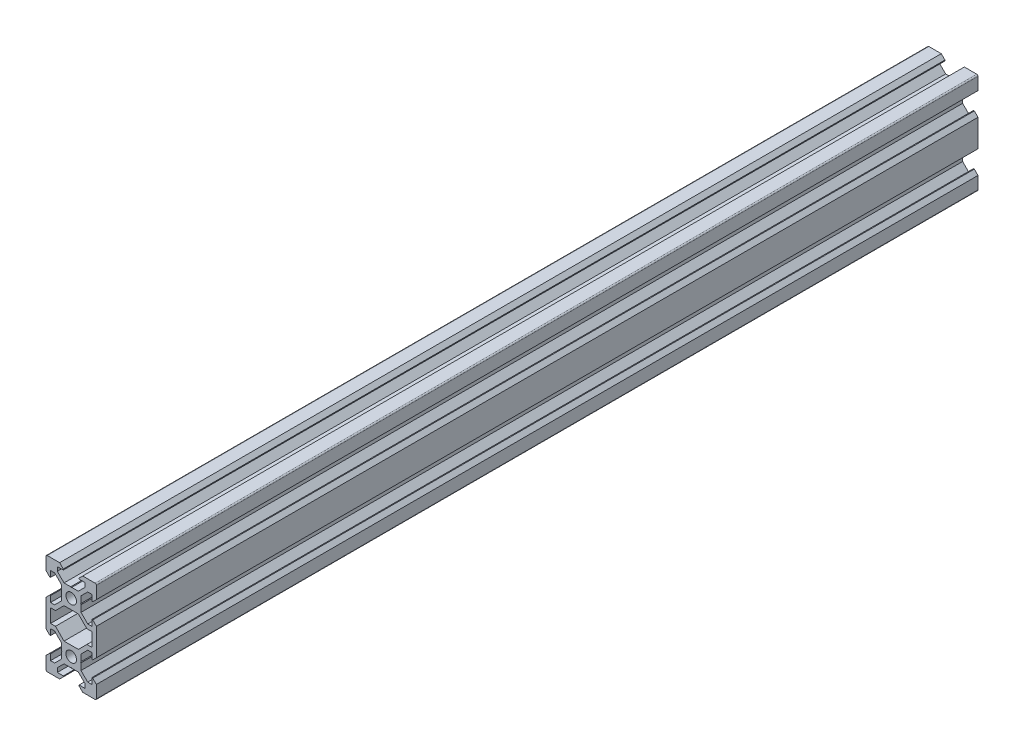
SolidWorks part; units mm, degrees
material "6061-T6 (SS)"
ref_plane "Front Plane" through (0, 0, 0) normal (0, 0, 1) x (1, 0, 0)
ref_plane "Top Plane" through (0, 0, 0) normal (0, 1, 0) x (1, 0, 0)
ref_plane "Right Plane" through (0, 0, 0) normal (1, 0, 0) x (0, 0, -1)
sketch "Sketch1" plane through (0, 0, 0) normal (0, 0, 1) x (1, 0, 0)
  line L0 (0, 0) -> (10, 0) construction
  line L1 (9.5, -20) -> (-9.5, -20)
  line L2 (10, -19.5) -> (10, 19.5)
  line L3 (9.5, 20) -> (-9.5, 20)
  line L4 (-10, -19.5) -> (-10, 19.5)
  line L5 (10, -20) -> (-10, 20) construction
  line L6 (10, 20) -> (-10, -20) construction
  circle A0 centre (0, 10) radius 2.1
  circle A1 centre (0, -10) radius 2.1
  arc A2 (-9.5, -20) -> (-10, -19.5) centre (-9.5, -19.5) cw
  arc A3 (9.5, -20) -> (10, -19.5) centre (9.5, -19.5) ccw
  arc A4 (10, 19.5) -> (9.5, 20) centre (9.5, 19.5) ccw
  arc A5 (-9.5, 20) -> (-10, 19.5) centre (-9.5, 19.5) ccw
  point P0 (0, 0)
  line B0 (0, 10) -> (0, 20) construction
  line B1 (0, 13.69) -> (-0.21, 13.9)
  line B2 (-0.21, 13.9) -> (-2.8393, 13.9)
  line B3 (-2.8393, 13.9) -> (-5.5, 16.5607)
  line B4 (-5.5, 16.5607) -> (-5.5, 18.2)
  line B5 (-5.5, 18.2) -> (-3.125, 18.2)
  line B6 (-3.125, 18.2) -> (-3.125, 18.545)
  line B7 (-3.125, 18.545) -> (-4.58, 20)
  line B8 (-4.58, 20) -> (4.58, 20)
  line B9 (0, 10) -> (-5.9132, 15.9132) construction
  line B10 (3.125, 18.545) -> (4.58, 20)
  line B11 (3.125, 18.2) -> (3.125, 18.545)
  line B12 (5.5, 18.2) -> (3.125, 18.2)
  line B13 (5.5, 16.5607) -> (5.5, 18.2)
  line B14 (2.8393, 13.9) -> (5.5, 16.5607)
  line B15 (0.21, 13.9) -> (2.8393, 13.9)
  line B16 (0, 13.69) -> (0.21, 13.9)
  line B17 (0, 10) -> (-10, 10) construction
  line B18 (-3.69, 10) -> (-3.9, 9.79)
  line B19 (-3.9, 9.79) -> (-3.9, 7.1607)
  line B20 (-3.9, 7.1607) -> (-6.5607, 4.5)
  line B21 (-6.5607, 4.5) -> (-8.2, 4.5)
  line B22 (-8.2, 4.5) -> (-8.2, 6.875)
  line B23 (-8.2, 6.875) -> (-8.545, 6.875)
  line B24 (-8.545, 6.875) -> (-10, 5.42)
  line B25 (-10, 5.42) -> (-10, 14.58)
  line B26 (0, 10) -> (-5.9132, 4.0868) construction
  line B27 (-8.545, 13.125) -> (-10, 14.58)
  line B28 (-8.2, 13.125) -> (-8.545, 13.125)
  line B29 (-8.2, 15.5) -> (-8.2, 13.125)
  line B30 (-6.5607, 15.5) -> (-8.2, 15.5)
  line B31 (-3.9, 12.8393) -> (-6.5607, 15.5)
  line B32 (-3.9, 10.21) -> (-3.9, 12.8393)
  line B33 (-3.69, 10) -> (-3.9, 10.21)
  line B34 (0, -10) -> (-10, -10) construction
  line B35 (-3.69, -10) -> (-3.9, -10.21)
  line B36 (-3.9, -10.21) -> (-3.9, -12.8393)
  line B37 (-3.9, -12.8393) -> (-6.5607, -15.5)
  line B38 (-6.5607, -15.5) -> (-8.2, -15.5)
  line B39 (-8.2, -15.5) -> (-8.2, -13.125)
  line B40 (-8.2, -13.125) -> (-8.545, -13.125)
  line B41 (-8.545, -13.125) -> (-10, -14.58)
  line B42 (-10, -14.58) -> (-10, -5.42)
  line B43 (0, -10) -> (-5.9132, -15.9132) construction
  line B44 (-8.545, -6.875) -> (-10, -5.42)
  line B45 (-8.2, -6.875) -> (-8.545, -6.875)
  line B46 (-8.2, -4.5) -> (-8.2, -6.875)
  line B47 (-6.5607, -4.5) -> (-8.2, -4.5)
  line B48 (-3.9, -7.1607) -> (-6.5607, -4.5)
  line B49 (-3.9, -9.79) -> (-3.9, -7.1607)
  line B50 (-3.69, -10) -> (-3.9, -9.79)
  line B51 (0, -10) -> (0, -20) construction
  line B52 (0, -13.69) -> (0.21, -13.9)
  line B53 (0.21, -13.9) -> (2.8393, -13.9)
  line B54 (2.8393, -13.9) -> (5.5, -16.5607)
  line B55 (5.5, -16.5607) -> (5.5, -18.2)
  line B56 (5.5, -18.2) -> (3.125, -18.2)
  line B57 (3.125, -18.2) -> (3.125, -18.545)
  line B58 (3.125, -18.545) -> (4.58, -20)
  line B59 (4.58, -20) -> (-4.58, -20)
  line B60 (0, -10) -> (5.9132, -15.9132) construction
  line B61 (-3.125, -18.545) -> (-4.58, -20)
  line B62 (-3.125, -18.2) -> (-3.125, -18.545)
  line B63 (-5.5, -18.2) -> (-3.125, -18.2)
  line B64 (-5.5, -16.5607) -> (-5.5, -18.2)
  line B65 (-2.8393, -13.9) -> (-5.5, -16.5607)
  line B66 (-0.21, -13.9) -> (-2.8393, -13.9)
  line B67 (0, -13.69) -> (-0.21, -13.9)
  line B68 (0, -10) -> (10, -10) construction
  line B69 (3.69, -10) -> (3.9, -9.79)
  line B70 (3.9, -9.79) -> (3.9, -7.1607)
  line B71 (3.9, -7.1607) -> (6.5607, -4.5)
  line B72 (6.5607, -4.5) -> (8.2, -4.5)
  line B73 (8.2, -4.5) -> (8.2, -6.875)
  line B74 (8.2, -6.875) -> (8.545, -6.875)
  line B75 (8.545, -6.875) -> (10, -5.42)
  line B76 (10, -5.42) -> (10, -14.58)
  line B77 (0, -10) -> (5.9132, -4.0868) construction
  line B78 (8.545, -13.125) -> (10, -14.58)
  line B79 (8.2, -13.125) -> (8.545, -13.125)
  line B80 (8.2, -15.5) -> (8.2, -13.125)
  line B81 (6.5607, -15.5) -> (8.2, -15.5)
  line B82 (3.9, -12.8393) -> (6.5607, -15.5)
  line B83 (3.9, -10.21) -> (3.9, -12.8393)
  line B84 (3.69, -10) -> (3.9, -10.21)
  line B85 (0, 10) -> (10, 10) construction
  line B86 (3.69, 10) -> (3.9, 10.21)
  line B87 (3.9, 10.21) -> (3.9, 12.8393)
  line B88 (3.9, 12.8393) -> (6.5607, 15.5)
  line B89 (6.5607, 15.5) -> (8.2, 15.5)
  line B90 (8.2, 15.5) -> (8.2, 13.125)
  line B91 (8.2, 13.125) -> (8.545, 13.125)
  line B92 (8.545, 13.125) -> (10, 14.58)
  line B93 (10, 14.58) -> (10, 5.42)
  line B94 (0, 10) -> (5.9132, 15.9132) construction
  line B95 (8.545, 6.875) -> (10, 5.42)
  line B96 (8.2, 6.875) -> (8.545, 6.875)
  line B97 (8.2, 4.5) -> (8.2, 6.875)
  line B98 (6.5607, 4.5) -> (8.2, 4.5)
  line B99 (3.9, 7.1607) -> (6.5607, 4.5)
  line B100 (3.9, 9.79) -> (3.9, 7.1607)
  line B101 (3.69, 10) -> (3.9, 9.79)
  line B102 (-8.2, -2.7) -> (-8.2, 2.7)
  line B103 (-8.2, 2.7) -> (-6.2393, 2.7)
  line B104 (-6.2393, 2.7) -> (-2.8393, 6.1)
  line B105 (-2.8393, 6.1) -> (2.8393, 6.1)
  line B106 (0, 6.1) -> (0, 0) construction
  line B107 (0, 0) -> (-8.2, 0) construction
  line B108 (6.2393, 2.7) -> (2.8393, 6.1)
  line B109 (8.2, 2.7) -> (6.2393, 2.7)
  line B110 (8.2, -2.7) -> (8.2, 2.7)
  line B111 (8.2, -2.7) -> (6.2393, -2.7)
  line B112 (6.2393, -2.7) -> (2.8393, -6.1)
  line B113 (-2.8393, -6.1) -> (2.8393, -6.1)
  line B114 (-6.2393, -2.7) -> (-2.8393, -6.1)
  line B115 (-8.2, -2.7) -> (-6.2393, -2.7)
  line B116 (0, 6.1) -> (0, 10) construction
  line B117 (0, 10) -> (-5.0927, 4.9073) construction
  dimension "D4" = 4.2
  dimension "D5" = 0.5
  dimension "D1" = 20
  dimension "D2" = 40
  dimension "D3" = 20
sketch_block_instance "V Slot 1-4"
sketch_block "V Slot 1" parameters "D1"=10, "D2"=11, "D3"=4.3, "D4"=1.8, "D5"=0.21, "D6"=45, "D7"=9.16, "D8"=1.5, "D9"=6.25
sketch_block_instance "V Slot 1-5"
sketch_block_instance "V Slot 1-6"
sketch_block_instance "V Slot 1-7"
sketch_block_instance "V Slot 1-8"
sketch_block_instance "V Slot 1-9"
sketch_block_instance "Center Cutout 1-1"
sketch_block "Center Cutout 1" parameters "D1"=5.4, "D2"=12.2, "D3"=8.2, "D4"=45, "D5"=10, "D6"=1.5
extrude "Boss-Extrude1" add sketch "Sketch1" along normal blind 350 contours B101 B86 B87 B88 B89 B90 B91 B92 L2 A4 L3 B10 B11 B12 B13 B14 B15 B16 B1 B2 B3 B4 B5 B6 B7 A5 L4 B27 B28 B29 B30 B31 B32 B33 B18 B19 B20 B21 B22 B23 B24 B44 B45 B46 B47 B48 B49 B50 B35
